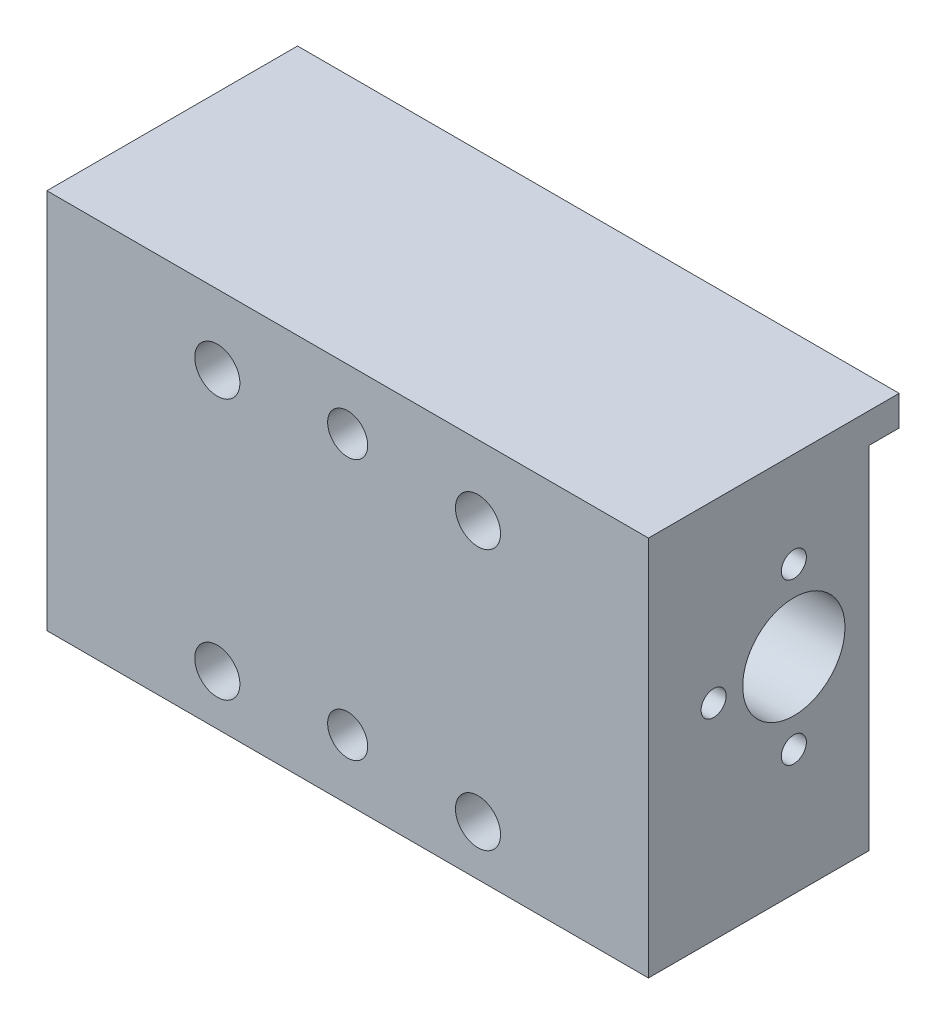
SolidWorks part; units mm, degrees
ref_plane "Alzado" through (0, 0, 0) normal (0, 0, 1) x (1, 0, 0)
ref_plane "Planta" through (0, 0, 0) normal (0, 1, 0) x (1, 0, 0)
ref_plane "Vista lateral" through (0, 0, 0) normal (1, 0, 0) x (0, 0, -1)
sketch "Croquis1" plane through (0, 0, 0) normal (0, 0, 1) x (1, 0, 0)
  line L1 (0, 0) -> (60, 0)
  line L2 (0, 0) -> (0, 38)
  line L3 (0, 38) -> (60, 38)
  line L4 (60, 0) -> (60, 38)
  dimension "D1" = 38
  dimension "D2" = 60
extrude "Saliente-Extruir1" add sketch "Croquis1" along normal blind 22
sketch "Croquis2" plane through (60, 0, 0) normal (1, 0, 0) x (0, 0, -1)
  line L1 (-22, 0) -> (-22, 38) construction
  line L2 (-22, 38) -> (0, 38) construction
  circle A0 centre (-7.5, 20.5) radius 5.1
  dimension "D1" = 10.2
  dimension "D2" = 14.5
  dimension "D3" = 17.5
extrude "Cortar-Extruir1" cut sketch "Croquis2" against normal through all
hole_wizard "Taladros de espiga de Ø4.0mm2" positions "Croquis4" profile "Croquis5" hole size "Ø4.0" standard "DIN"
sketch "Croquis4" plane through (0, 0, 22) normal (0, 0, 1) x (1, 0, 0)
  line L0 (0, 32) -> (60, 32) construction
  line L1 (0, 38) -> (0, 0) construction
  line L2 (60, 0) -> (60, 38) construction
  line L5 (60, 6) -> (0, 6) construction
  line L7 (60, 38) -> (0, 38) construction
  line L8 (30, 38) -> (30, 0) construction
  line L9 (0, 0) -> (60, 0) construction
  point P24 (30, 32)
  point P26 (30, 6)
  dimension "D1" = 6
  dimension "D2" = 6
sketch "Croquis5" plane through (30, 6, 22) normal (1, 0, 0) x (0, -1, 0)
  line L0 (0, 0) -> (0, 15.2017)
  line L1 (0, 15.2017) -> (2, 14)
  line L2 (2, 14) -> (2, 0)
  line L5 (2, 0) -> (0, 0)
  line L10 (0, 15.2017) -> (-2, 14) construction
  line L11 (0, -6.35) -> (0, 107.95) construction
  dimension "Diámetro de taladro" = 4
  dimension "Profundidad de taladro" = 14
  dimension "Ángulo de perforador" = 118
sketch "Croquis6" plane through (0, 0, 0) normal (0, 0, -1) x (-1, 0, 0)
  line L1 (-60, 35) -> (0, 35)
  line L2 (-60, 35) -> (-60, 38)
  line L3 (-60, 38) -> (0, 38)
  line L4 (0, 35) -> (0, 38)
  dimension "D1" = 3
  dimension "D2" = 60
extrude "Saliente-Extruir2" add sketch "Croquis6" along normal blind 3
hole_wizard "Taladro roscado M31" positions "Croquis10" profile "Croquis11" tap size "M3" standard "DIN"
sketch "Croquis10" plane through (60, 0, 0) normal (1, 0, 0) x (0, 0, -1)
  line L0 (-7.5, 12.5) -> (-7.5, 28.5) construction
  line L2 (-15.5, 20.5) -> (-7.5, 20.5) construction
  circle A0 centre (-7.5, 20.5) radius 8 construction
  point P5 (-7.5, 12.5)
  point P6 (-7.5, 28.5)
  point P8 (-15.5, 20.5)
  dimension "D1" = 16
sketch "Croquis11" plane through (60, 20.5, 15.5) normal (0, 1, 0) x (0, 0, -1)
  line L0 (0, 0) -> (0, 14.7511)
  line L1 (0, 14.7511) -> (1.25, 14)
  line L2 (1.25, 14) -> (1.25, 0)
  line L5 (1.25, 0) -> (0, 0)
  line L10 (0, 14.7511) -> (-1.25, 14) construction
  line L11 (0, -6.35) -> (0, 107.95) construction
  dimension "Diámetro de perforador para roscar" = 2.5
  dimension "Profundidad de perforador para roscar" = 14
  dimension "Ángulo de perforador" = 118
cosmetic thread "Rosca de taladro1" parameters "D1"=6, "D2"=3
cosmetic thread "Rosca de taladro2" parameters "D1"=6, "D2"=3
cosmetic thread "Rosca de taladro3" parameters "D1"=6, "D2"=3
hole_wizard "Taladro de margen para M41" positions "Croquis12" profile "Croquis14" hole size "M4" standard "DIN" end condition through all
sketch "Croquis12" plane through (0, 0, 22) normal (0, 0, 1) x (1, 0, 0)
  line L12 (43, 31) -> (17, 31) construction
  line L13 (43, 31) -> (43, 5) construction
  line L14 (43, 5) -> (17, 5) construction
  line L15 (17, 31) -> (17, 5) construction
  line L16 (43, 31) -> (17, 5) construction
  line L17 (43, 5) -> (17, 31) construction
  line L18 (0, 0) -> (60, 0) construction
  line L19 (60, 0) -> (60, 38) construction
  point P0 (43, 5)
  point P2 (43, 31)
  point P4 (17, 5)
  point P6 (17, 31)
  point P155 (0, 0)
  point P156 (0, 0)
  point P157 (30, 18)
  dimension "D1" = 26
  dimension "D2" = 26
  dimension "D3" = 18
  dimension "D4" = 30
sketch "Croquis14" plane through (43, 5, 22) normal (1, 0, 0) x (0, -1, 0)
  line L0 (0, 0) -> (0, 25)
  line L1 (0, 25) -> (2.25, 25)
  line L2 (2.25, 25) -> (2.25, 0)
  line L5 (2.25, 0) -> (0, 0)
  line L11 (0, -6.35) -> (0, 107.95) construction
  dimension "Diámetro de taladro hasta el siguiente" = 4.5
  dimension "Profundidad de taladro hasta el siguiente" = 25
